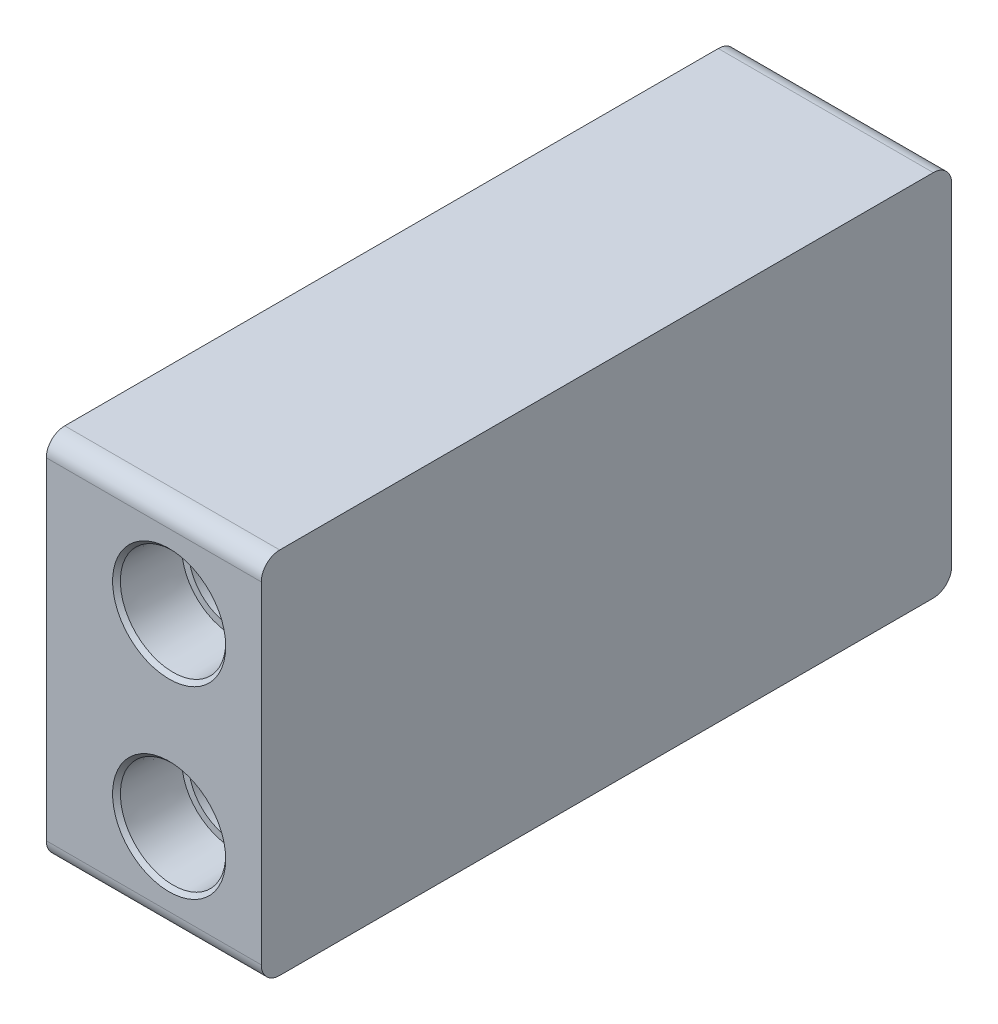
SolidWorks part; units mm, degrees
material "6061 Alloy"
ref_plane "Front Plane" through (0, 0, 0) normal (0, 0, 1) x (1, 0, 0)
ref_plane "Top Plane" through (0, 0, 0) normal (0, 1, 0) x (1, 0, 0)
ref_plane "Right Plane" through (0, 0, 0) normal (1, 0, 0) x (0, 0, -1)
sketch "block_sketch" plane through (0, 0, 0) normal (1, 0, 0) x (0, 0, -1)
  line L1 (56.2034, 30) -> (-56.2034, 30)
  line L2 (56.2034, 30) -> (56.2034, -30)
  line L3 (56.2034, -30) -> (-56.2034, -30)
  line L4 (-56.2034, 30) -> (-56.2034, -30)
  line L5 (56.2034, 30) -> (-56.2034, -30) construction
  line L6 (56.2034, -30) -> (-56.2034, 30) construction
  point P0 (0, 0)
  dimension "D1" = 60
extrude "block" add sketch "block_sketch" along normal mid plane 35
hole_wizard "3/8 NPT_flow_connector" positions "Sketch5" profile "Sketch6" size "3/8" standard "ANSI Inch"
sketch "Sketch5" plane through (0, 0, 56.2034) normal (0, 0, 1) x (1, 0, 0)
  line L3 (-17.5, 0) -> (17.5, 0) construction
  line L4 (-17.5, 30) -> (-17.5, -30) construction
  line L5 (17.5, 30) -> (17.5, -30) construction
  line L11 (2.5, -30) -> (2.5, 30) construction
  line L12 (17.5, -30) -> (-17.5, -30) construction
  line L13 (17.5, 30) -> (-17.5, 30) construction
  circle A0 centre (2.5, -15) radius 15 construction
  circle A1 centre (2.5, 15) radius 15 construction
  point P8 (2.5, 15)
  point P10 (2.5, -15)
  dimension "D3" = 30
  dimension "D1" = 30
  dimension "D2" = 20
sketch "Sketch6" plane through (2.5, 15, 56.2034) normal (1, 0, 0) x (0, -1, 0)
  line L0 (0, 0) -> (0, 21.6686)
  line L1 (7.1374, 17.38) -> (0, 21.6686)
  line L2 (-7.1374, 17.38) -> (0, 21.6686) construction
  line L3 (7.1374, 17.38) -> (7.1374, 10.33)
  line L4 (7.1374, 10.33) -> (8.2822, 10.33)
  line L5 (8.2822, 10.33) -> (8.5725, 0.635)
  line L6 (8.5725, 0.635) -> (9.2075, 0)
  line L7 (9.2075, 0) -> (0, 0)
  line L8 (0, -6.35) -> (0, 107.95) construction
  line L9 (-8.5725, 0.635) -> (-9.2075, 0) construction
  line L11 (-7.1374, 10.33) -> (-8.2822, 10.33) construction
  line L12 (-8.2822, 10.33) -> (-8.5725, 0.635) construction
  dimension "Tap Drill Dia." = 14.2748
  dimension "Tap Drill Depth" = 17.38
  dimension "Thread Dia." = 17.145
  dimension "Thread Angle" = 3.43
  dimension "Thread Depth" = 10.33
  dimension "C'Sink Dia." = 18.415
  dimension "C'Sink Angle" = 90
  dimension "Drill Angle" = 118
hole_wizard "M8_flow_channel" positions "Sketch14" profile "Sketch15" hole size "1/2" standard "ANSI Inch"
sketch "Sketch14" plane through (0, 0, 56.2034) normal (0, 0, 1) x (1, 0, 0)
  point P3 (2.5, -15)
  point P7 (0, 0)
sketch "Sketch15" plane through (2.5, -15, 56.2034) normal (1, 0, 0) x (0, -1, 0)
  line L0 (0, 0) -> (0, 42.0189)
  line L1 (0, 42.0189) -> (6.35, 38.2034)
  line L2 (6.35, 38.2034) -> (6.35, 0)
  line L5 (6.35, 0) -> (0, 0)
  line L10 (0, 42.0189) -> (-6.35, 38.2034) construction
  line L11 (0, -6.35) -> (0, 107.95) construction
  dimension "Hole Dia." = 12.7
  dimension "Hole Depth" = 38.2034
  dimension "Drill Angle" = 118
hole_wizard "M10_flow_channel" positions "Sketch19" profile "Sketch20" hole size "1/2" standard "ANSI Inch"
sketch "Sketch19" plane through (0, 0, 56.2034) normal (0, 0, 1) x (1, 0, 0)
  point P0 (2.5, 15)
sketch "Sketch20" plane through (2.5, 15, 56.2034) normal (1, 0, 0) x (0, -1, 0)
  line L0 (0, 0) -> (0, 42.0189)
  line L1 (0, 42.0189) -> (6.35, 38.2034)
  line L2 (6.35, 38.2034) -> (6.35, 0)
  line L5 (6.35, 0) -> (0, 0)
  line L10 (0, 42.0189) -> (-6.35, 38.2034) construction
  line L11 (0, -6.35) -> (0, 107.95) construction
  dimension "Hole Dia." = 12.7
  dimension "Hole Depth" = 38.2034
  dimension "Drill Angle" = 118
mirror "flow_mirror" about plane through (0, 0, 0) normal (0, 0, 1) of "M10_flow_channel", "3/8 NPT_flow_connector", "M8_flow_channel"
hole_wizard "1/8 NPT_pressure_sensor_connector" positions "Sketch3" profile "Sketch4" size "1/8" standard "ANSI Inch"
sketch "Sketch3" plane through (-17.5, 14.5969, 0) normal (1, 0, 0) x (0, -1, 0)
  line L11 (-0.4031, 56.2034) -> (-0.4031, -56.2034) construction
  line L12 (44.5969, 56.2034) -> (-15.4031, 56.2034) construction
  line L14 (29.5969, 56.2034) -> (29.5969, -56.2034) construction
  line L15 (-15.4031, -56.2034) -> (44.5969, -56.2034) construction
  line L20 (23.2469, 18) -> (35.9469, 18) construction
  line L26 (23.2469, -18) -> (35.9469, -18) construction
  circle A0 centre (29.5969, 21.1) radius 3.1 construction
  circle A1 centre (29.5969, -21.1) radius 3.1 construction
  circle A2 centre (29.5969, 21.1) radius 13.5 construction
  circle A3 centre (-0.4031, 21.1) radius 13.5 construction
  circle A4 centre (-0.4031, -21.1) radius 13.5 construction
  circle A5 centre (29.5969, -21.1) radius 13.5 construction
  point P0 (29.5969, -21.1)
  point P13 (29.5969, 21.1)
  point P69 (-0.4031, 21.1)
  point P71 (-0.4031, -21.1)
  dimension "D1" = 6.2
  dimension "D2" = 27
sketch "Sketch4" plane through (-17.5, -15, 21.1) normal (0, 1, 0) x (0, 0, 1)
  line L0 (0, 0) -> (0, 14.1535)
  line L1 (4.2164, 11.62) -> (0, 14.1535)
  line L2 (-4.2164, 11.62) -> (0, 14.1535) construction
  line L3 (4.2164, 11.62) -> (4.2164, 6.92)
  line L4 (4.2164, 6.92) -> (4.9552, 6.92)
  line L5 (4.9552, 6.92) -> (5.1434, 0.635)
  line L6 (5.1434, 0.635) -> (5.7784, 0)
  line L7 (5.7784, 0) -> (0, 0)
  line L8 (0, -6.35) -> (0, 107.95) construction
  line L9 (-5.1434, 0.635) -> (-5.7784, 0) construction
  line L11 (-4.2164, 6.92) -> (-4.9552, 6.92) construction
  line L12 (-4.9552, 6.92) -> (-5.1434, 0.635) construction
  dimension "Tap Drill Dia." = 8.4328
  dimension "Tap Drill Depth" = 11.62
  dimension "Thread Dia." = 10.2867
  dimension "Thread Angle" = 3.43
  dimension "Thread Depth" = 6.92
  dimension "C'Sink Dia." = 11.5567
  dimension "C'Sink Angle" = 90
  dimension "Drill Angle" = 118
sketch "Sketch11" plane through (-17.5, 14.5969, 0) normal (1, 0, 0) x (0, -1, 0)
  circle A0 centre (29.5969, 21.1) radius 1.6
  circle A1 centre (29.5969, -21.1) radius 1.6
  circle A2 centre (-0.4031, 21.1) radius 1.6
  circle A3 centre (-0.4031, -21.1) radius 1.6
  circle A4 centre (-0.4031, 21.1) radius 4.2164 construction
  point P12 (0, 0)
  point P13 (29.5969, 21.1)
  point P15 (0, 0)
  point P16 (0, 0)
  dimension "D1" = 3.2
extrude "pressure_sensor_hole" cut sketch "Sketch11" along normal up to next
hole_wizard "M8x1.0 Tapped Hole1" positions "Sketch9" profile "Sketch10" tap size "M8x1.0" standard "ANSI Metric" end condition through all
sketch "Sketch9" plane through (0, 0, 56.2034) normal (0, 0, 1) x (1, 0, 0)
  point P3 (2.5, -15)
cosmetic thread "Hole Thread1" parameters "D2"=8
sketch "Sketch10" plane through (2.5, -15, 56.2034) normal (1, 0, 0) x (0, -1, 0)
  line L0 (0, 0) -> (0, 112.4068)
  line L1 (0, 112.4068) -> (3.5, 112.4068)
  line L2 (3.5, 112.4068) -> (3.5, 0)
  line L5 (3.5, 0) -> (0, 0)
  line L11 (0, -6.35) -> (0, 107.95) construction
  dimension "Thru Tap Drill Dia." = 7
  dimension "Thru Tap Drill Depth" = 112.4068
hole_wizard "M10x1.0 Tapped Hole1" positions "Sketch12" profile "Sketch13" tap size "M10x1.0" standard "ANSI Metric" end condition through all
sketch "Sketch12" plane through (0, 0, 56.2034) normal (0, 0, 1) x (1, 0, 0)
  point P0 (2.5, 15)
sketch "Sketch13" plane through (2.5, 15, 56.2034) normal (1, 0, 0) x (0, -1, 0)
  line L0 (0, 0) -> (0, 112.4068)
  line L1 (0, 112.4068) -> (4.5, 112.4068)
  line L2 (4.5, 112.4068) -> (4.5, 0)
  line L5 (4.5, 0) -> (0, 0)
  line L11 (0, -6.35) -> (0, 107.95) construction
  dimension "Thru Tap Drill Dia." = 9
  dimension "Thru Tap Drill Depth" = 112.4068
cosmetic thread "Hole Thread3" parameters "D2"=10
fillet "rounded_edges" radius 3 4 edges at (0, -30, 56.2034) (0, 30, 56.2034) (0, 30, -56.2034) (0, -30, -56.2034)
equation "\"pressure_hole_diameter\"= 3.2mm"
equation "\"D1@Sketch11\"=\"pressure_hole_diameter\""
equation "\"D1@Sketch3\"=\"pressure_hole_diameter\"+\"pressure_hole_offset\""
equation "\"pressure_hole_offset\"= 3mm"
equation "\"flow_channel_spacing\" = 30mm"
equation "\"D1@Sketch5\"=\"flow_channel_spacing\""
equation "\"flow_channel_offset\"= 20mm"
equation "\"flow_connector_keepout\"= 30mm"
equation "\"D3@Sketch5\"=\"flow_connector_keepout\""
equation "\"D2@Sketch5\"=\"flow_channel_offset\""
equation "\"D1@block_sketch\"=\"flow_connector_keepout\"*2"
equation "\"D1@block\"=\"flow_connector_keepout\"/2+\"flow_channel_offset\""
equation "\"pressure_sensor_keepout\" = 27mm"
equation "\"D2@Sketch3\"=\"pressure_sensor_keepout\""
